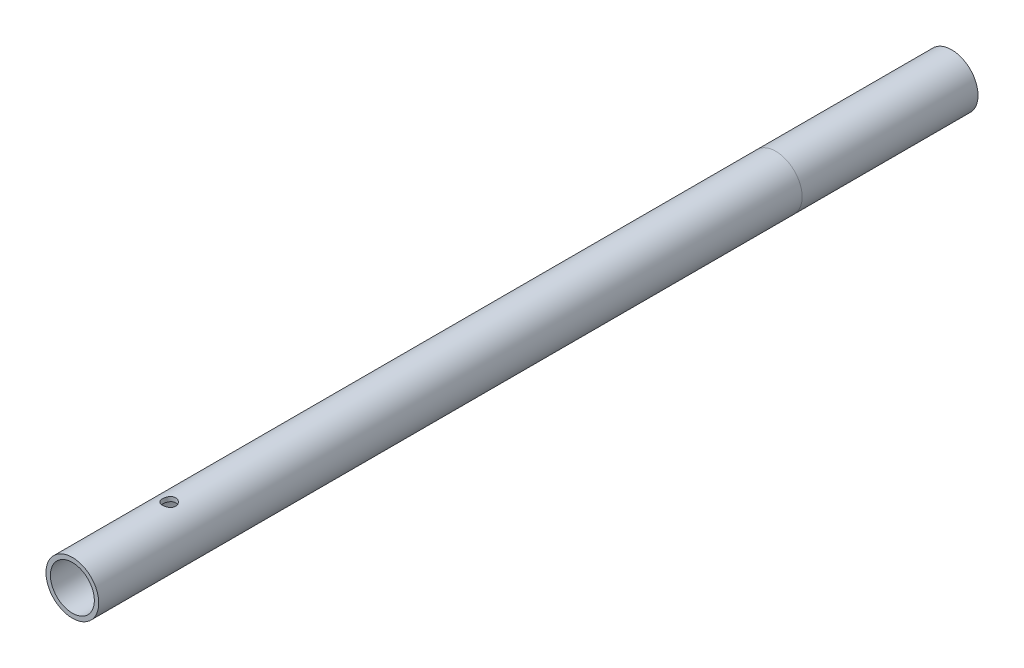
SolidWorks part; units mm, degrees
material "1060 Alloy"
ref_plane "Ön Düzlem" through (0, 0, 0) normal (0, 0, 1) x (1, 0, 0)
ref_plane "Üst Düzlem" through (0, 0, 0) normal (0, 1, 0) x (1, 0, 0)
ref_plane "Sağ Düzlem" through (0, 0, 0) normal (1, 0, 0) x (0, 0, -1)
sketch "Sketch1" plane through (0, 0, 0) normal (0, 0, 1) x (1, 0, 0)
  circle A0 centre (0, 0) radius 6
  circle A2 centre (0, 0) radius 5
  dimension "D1" = 12
  dimension "D2" = 1
extrude "Boss-Extrude1" add sketch "Sketch1" along normal blind 200
sketch "Sketch2" plane through (0, 0, 0) normal (0, 1, 0) x (1, 0, 0)
  line L0 (-15, -40) -> (15, -40)
  point P4 (0, -40)
  dimension "D1" = 40
  dimension "D2" = 30
split line "Split Line2"
sketch "Sketch3" plane through (0, 0, 0) normal (0, 1, 0) x (1, 0, 0)
  line L1 (-6, -200) -> (6, -200) construction
  circle A2 centre (0, -178) radius 1.5
  dimension "D1" = 3
  dimension "D2" = 22
extrude "Cut-Extrude1" cut sketch "Sketch3" against normal through all both and the other way through all
equation "\"motor_r\"= 35 / 2mm"
equation "\"boru_d\"= 12mm"
equation "\"D1@Sketch1\"=\"boru_d\""
